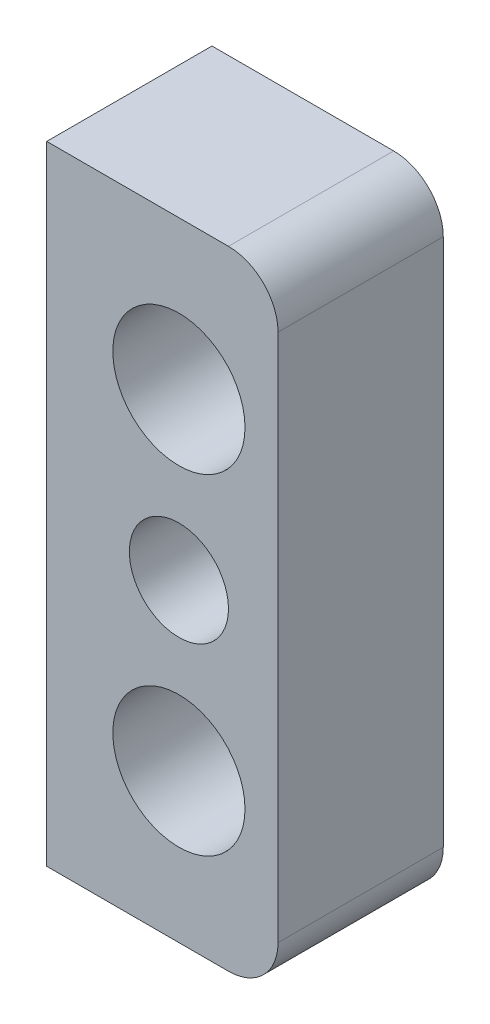
SolidWorks part; units mm, degrees
ref_plane "Front Plane" through (0, 0, 0) normal (0, 0, 1) x (1, 0, 0)
ref_plane "Top Plane" through (0, 0, 0) normal (0, 1, 0) x (1, 0, 0)
ref_plane "Right Plane" through (0, 0, 0) normal (1, 0, 0) x (0, 0, -1)
sketch "Sketch1" plane through (0, 0, 0) normal (0, 0, 1) x (1, 0, 0)
  line L0 (20, -9.5) -> (20, 9.5)
  line L1 (20, -9.5) -> (25.5, -9.5)
  line L2 (20, 9.5) -> (25.5, 9.5)
  line L3 (27, -8) -> (27, 8)
  line L5 (24, -9.5) -> (24, 9.5) construction
  circle A0 centre (24, 5) radius 2
  circle A1 centre (24, -5) radius 2
  circle A2 centre (24, 0) radius 1.5
  arc A6 (25.5, -9.5) -> (27, -8) centre (25.5, -8) ccw
  arc A7 (25.5, 9.5) -> (27, 8) centre (25.5, 8) cw
  point P9 (24, -5)
  point P10 (24, 5)
  dimension "D2" = 4
  dimension "D3" = 1.3667
  dimension "D1" = 1.5
  dimension "D5" = 2.6333
extrude "Boss-Extrude2" add sketch "Sketch1" against normal blind 5
